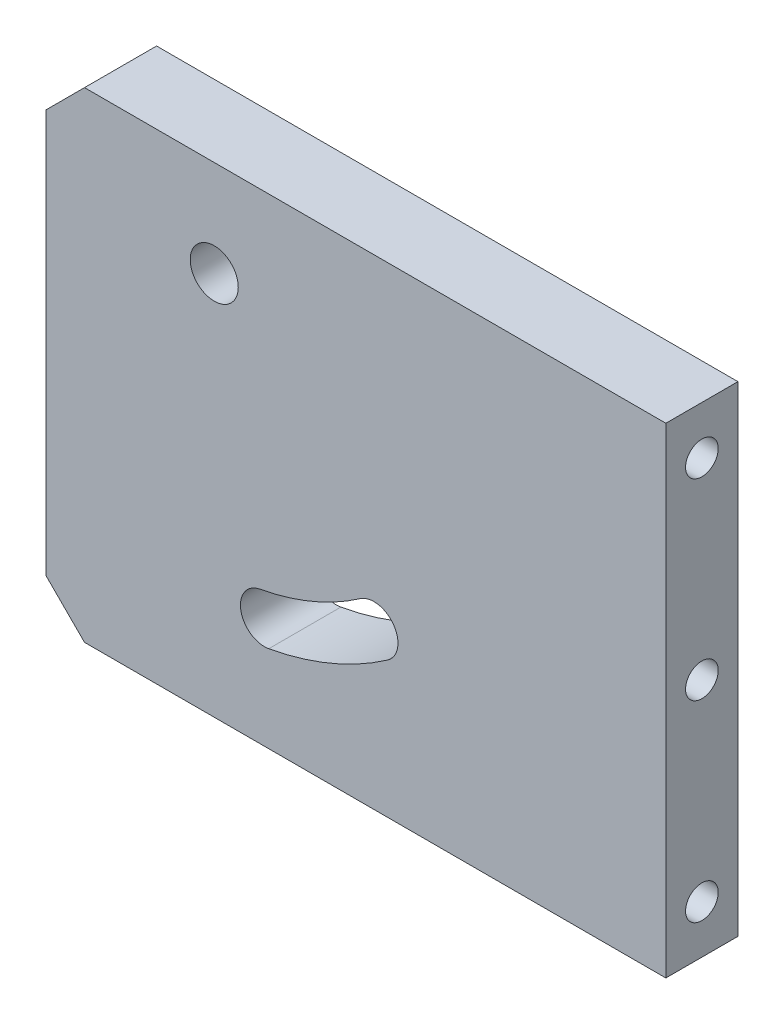
SolidWorks part; units mm, degrees
ref_plane "Alzado" through (0, 0, 0) normal (0, 0, 1) x (1, 0, 0)
ref_plane "Planta" through (0, 0, 0) normal (0, 1, 0) x (1, 0, 0)
ref_plane "Vista lateral" through (0, 0, 0) normal (1, 0, 0) x (0, 0, -1)
sketch "Croquis1" plane through (0, 0, 0) normal (0, 0, 1) x (1, 0, 0)
  line L0 (-64.5, 42) -> (-56.5, 50)
  line L1 (64.5, -50) -> (-56.5, -50)
  line L2 (64.5, -50) -> (64.5, 50)
  line L3 (64.5, 50) -> (-56.5, 50)
  line L4 (-64.5, -42) -> (-64.5, 42)
  line L5 (64.5, -50) -> (-64.5, 50) construction
  line L6 (64.5, 50) -> (-64.5, -50) construction
  line L7 (-64.5, -42) -> (-56.5, -50)
  line L8 (-29.5, 30) -> (3.7426, -17.5282) construction
  line L9 (-29.5, 30) -> (-19.0498, -27.0508) construction
  circle A0 centre (-29.5, 30) radius 5
  arc A1 (3.7426, -17.5282) -> (-19.0498, -27.0508) centre (-29.5, 30) cw construction
  arc A2 (-18.1489, -31.969) -> (6.6083, -21.6255) centre (-29.5, 30) ccw
  arc A3 (-19.9507, -22.1326) -> (0.8768, -13.431) centre (-29.5, 30) ccw
  arc A4 (-19.9507, -22.1326) -> (-18.1489, -31.969) centre (-19.0498, -27.0508) ccw
  arc A5 (6.6083, -21.6255) -> (0.8768, -13.431) centre (3.7426, -17.5282) ccw
  point P0 (0, 0)
  point P14 (-7.1408, -23.517)
  dimension "D11" = 10
  dimension "D14" = 58
  dimension "D15" = 5
  dimension "D1" = 129
  dimension "D2" = 100
  dimension "D3" = 8
  dimension "D4" = 8
  dimension "D5" = 8
  dimension "D6" = 8
  dimension "D7" = 64.5
  dimension "D8" = 50
  dimension "D9" = 50
  dimension "D10" = 135
  dimension "D12" = 35
  dimension "D13" = 20
  dimension "D16" = 10.38
  dimension "D17" = 24.59
  dimension "D18" = 45.4502
  dimension "D19" = 68.2426
  dimension "D20" = 22.9492
  dimension "D21" = 32.4718
extrude "Saliente-Extruir1" add sketch "Croquis1" along normal blind 15
hole_wizard "Taladro roscado M81" positions "Croquis3" profile "Croquis2" tap size "M8" standard "DIN"
sketch "Croquis3" plane through (64.5, 0, 0) normal (1, 0, 0) x (0, 0, -1)
  line L0 (-15, 50) -> (0, 50) construction
  line L1 (0, -50) -> (0, 50) construction
  line L2 (-15, -50) -> (0, -50) construction
  point P0 (-7.5, 40)
  point P3 (-7.5, 0)
  point P5 (-7.5, -40)
  dimension "D1" = 10
  dimension "D2" = 7.5
  dimension "D3" = 10
  dimension "D4" = 40
  dimension "D5" = 40
sketch "Croquis2" plane through (64.5, 40, 7.5) normal (0, 1, 0) x (0, 0, -1)
  line L0 (0, 0) -> (0, 22.0429)
  line L1 (0, 22.0429) -> (3.4, 20)
  line L2 (3.4, 20) -> (3.4, 0)
  line L5 (3.4, 0) -> (0, 0)
  line L10 (0, 22.0429) -> (-3.4, 20) construction
  line L11 (0, -6.35) -> (0, 107.95) construction
  dimension "Diámetro de perforador para roscar" = 6.8
  dimension "Profundidad de perforador para roscar" = 20
  dimension "Ángulo de perforador" = 118
cosmetic thread "Rosca de taladro1" parameters "D1"=16, "D2"=8
cosmetic thread "Rosca de taladro2" parameters "D1"=16, "D2"=8
cosmetic thread "Rosca de taladro3" parameters "D1"=16, "D2"=8
